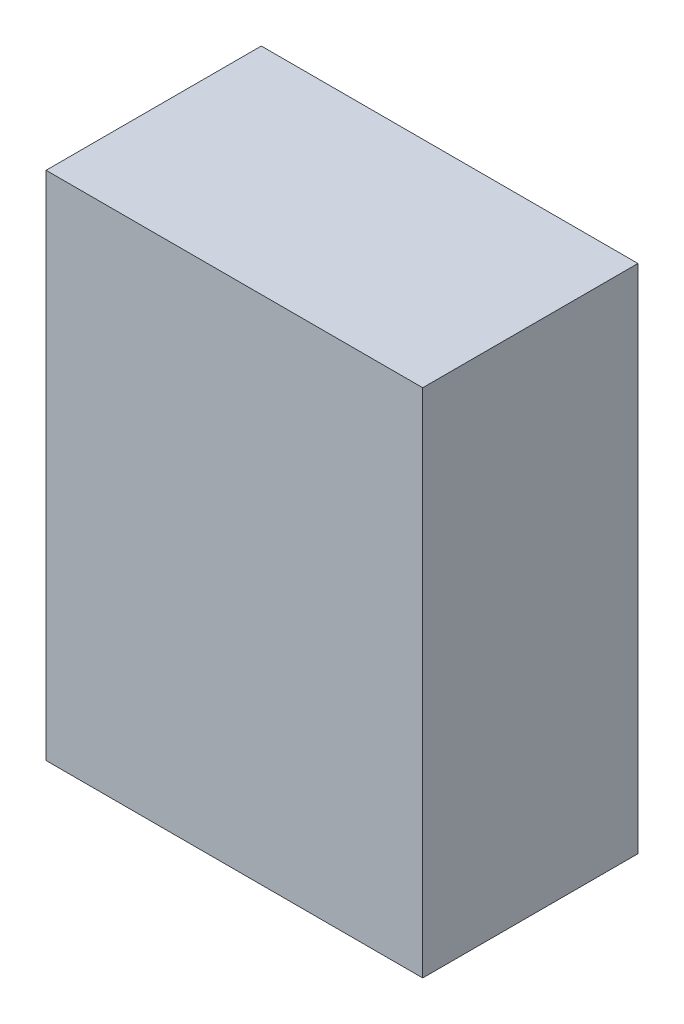
SolidWorks part; units mm, degrees
ref_plane "Plan de face" through (0, 0, 0) normal (0, 0, 1) x (1, 0, 0)
ref_plane "Plan de dessus" through (0, 0, 0) normal (0, 1, 0) x (1, 0, 0)
ref_plane "Plan de droite" through (0, 0, 0) normal (1, 0, 0) x (0, 0, -1)
sketch "Esquisse1" plane through (0, 0, 0) normal (0, 0, 1) x (1, 0, 0)
  line L1 (-150.969, 47.1318) -> (-80.969, 47.1318)
  line L2 (-150.969, 47.1318) -> (-150.969, -47.8682)
  line L3 (-150.969, -47.8682) -> (-80.969, -47.8682)
  line L4 (-80.969, 47.1318) -> (-80.969, -47.8682)
  line L5 (-150.969, 47.1318) -> (-80.969, -47.8682) construction
  line L6 (-150.969, -47.8682) -> (-80.969, 47.1318) construction
  point P4 (-115.969, -0.3682)
  dimension "D1" = 95
  dimension "D2" = 70
extrude "Boss.-Extru.1" add sketch "Esquisse1" along normal blind 40
